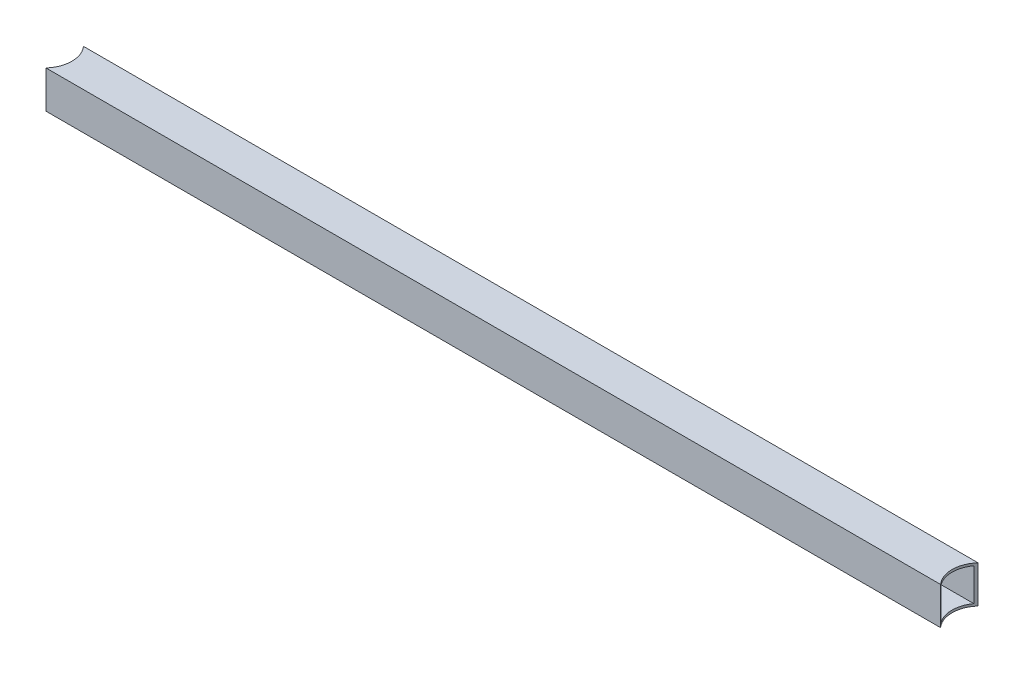
SolidWorks part; units mm, degrees
material "6061 Alloy"
ref_plane "Front Plane" through (0, 0, 0) normal (0, 0, 1) x (1, 0, 0)
ref_plane "Top Plane" through (0, 0, 0) normal (0, 1, 0) x (1, 0, 0)
ref_plane "Right Plane" through (0, 0, 0) normal (1, 0, 0) x (0, 0, -1)
sketch "Sketch1" plane through (0, 0, 0) normal (1, 0, 0) x (0, 0, -1)
  line L0 (0, 0) -> (1.5875, 1.5875) construction
  line L1 (0, 0) -> (25.4, 0)
  line L2 (0, 0) -> (0, 25.4)
  line L3 (0, 25.4) -> (25.4, 25.4)
  line L4 (25.4, 0) -> (25.4, 25.4)
  line L5 (1.5875, 1.5875) -> (23.8125, 1.5875)
  line L6 (1.5875, 1.5875) -> (1.5875, 23.8125)
  line L7 (1.5875, 23.8125) -> (23.8125, 23.8125)
  line L8 (23.8125, 1.5875) -> (23.8125, 23.8125)
  line L9 (23.8125, 23.8125) -> (25.4, 25.4) construction
  point P9 (0, 0)
  point P10 (23.6601, 1.7399)
  dimension "D1" = 25.4
  dimension "D2" = 25.4
  dimension "D3" = 1.5875
  dimension "D4" = 1.5875
extrude "Boss-Extrude1" add sketch "Sketch1" along normal blind 635
sketch "Sketch2" plane through (0, 25.4, 0) normal (0, 1, 0) x (1, 0, 0)
  line L0 (317.5, 0) -> (317.5, 25.4) construction
  line L1 (635, 0) -> (0, 0) construction
  line L2 (635, 25.4) -> (0, 25.4) construction
  line L3 (635, 12.7) -> (0, 12.7) construction
  line L4 (0, 25.4) -> (0, 0) construction
  circle A0 centre (0, 12.7) radius 19.05
  circle A1 centre (635, 12.7) radius 19.05
  point P11 (317.5, 12.7)
  dimension "D1" = 38.1
extrude "Cut-Extrude1" cut sketch "Sketch2" against normal through all
